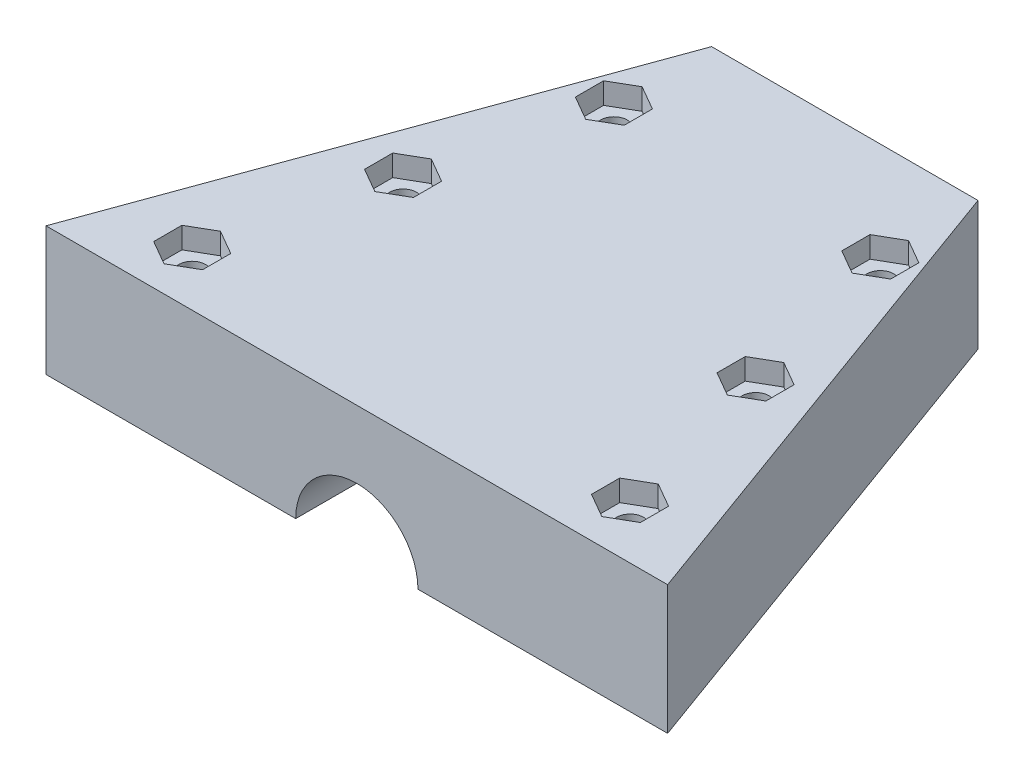
SolidWorks part; units mm, degrees
ref_plane "Front Plane" through (0, 0, 0) normal (0, 0, 1) x (1, 0, 0)
ref_plane "Top Plane" through (0, 0, 0) normal (0, 1, 0) x (1, 0, 0)
ref_plane "Right Plane" through (0, 0, 0) normal (1, 0, 0) x (0, 0, -1)
sketch "Sketch6" plane through (0, 0, 0) normal (0, 1, 0) x (1, 0, 0)
  line L0 (-16.8369, 5.7834) -> (13.1631, 5.7834)
  line L1 (13.1631, 5.7834) -> (33.1631, -49.1662)
  line L2 (33.1631, -49.1662) -> (-36.8369, -49.1662)
  line L3 (-36.8369, -49.1662) -> (-16.8369, 5.7834)
  circle A0 centre (13.1631, -5.2166) radius 1.78
  circle A1 centre (-16.8369, -5.2166) radius 1.78
  circle A2 centre (-26.4869, -43.0491) radius 1.78
  circle A3 centre (22.8131, -43.0491) radius 1.78
  dimension "D1" = 3.56
  dimension "D3" = 3.56
  dimension "D4" = 3.56
  dimension "D5" = 3.56
  dimension "D2" = 70
  dimension "D6" = 30
  dimension "D7" = 11
  dimension "D8" = 11
  dimension "D9" = 49.3
  dimension "D10" = 10.35
  dimension "D11" = 10.35
  dimension "D12" = 30
extrude "Boss-Extrude3" add sketch "Sketch6" along normal blind 14.5 contours L3 L0 L1 L2
sketch "Sketch8" plane through (0, 0, 49.1662) normal (0, 0, 1) x (1, 0, 0)
  line L0 (33.1631, 0) -> (-36.8369, 0) construction
  circle A0 centre (-1.8369, 0) radius 6.8846
extrude "Cut-Extrude3" cut sketch "Sketch8" against normal blind 88
sketch "Sketch9" plane through (0, 14.5, 0) normal (0, 1, 0) x (1, 0, 0)
  line L1 (-21.6619, -27.3083) -> (-18.9119, -25.7206)
  line L2 (-18.9119, -25.7206) -> (-18.9119, -22.5452)
  line L3 (-18.9119, -22.5452) -> (-21.6619, -20.9574)
  line L4 (-21.6619, -20.9574) -> (-24.4119, -22.5452)
  line L5 (-24.4119, -22.5452) -> (-24.4119, -25.7206)
  line L6 (-24.4119, -25.7206) -> (-21.6619, -27.3083)
  line L7 (-26.4869, -46.2245) -> (-23.7369, -44.6368)
  line L8 (-23.7369, -44.6368) -> (-23.7369, -41.4614)
  line L9 (-23.7369, -41.4614) -> (-26.4869, -39.8737)
  line L10 (-26.4869, -39.8737) -> (-29.2369, -41.4614)
  line L11 (-29.2369, -41.4614) -> (-29.2369, -44.6368)
  line L12 (-29.2369, -44.6368) -> (-26.4869, -46.2245)
  line L13 (22.8131, -46.2245) -> (25.5631, -44.6368)
  line L14 (25.5631, -44.6368) -> (25.5631, -41.4614)
  line L15 (25.5631, -41.4614) -> (22.8131, -39.8737)
  line L16 (22.8131, -39.8737) -> (20.0631, -41.4614)
  line L17 (20.0631, -41.4614) -> (20.0631, -44.6368)
  line L18 (20.0631, -44.6368) -> (22.8131, -46.2245)
  line L19 (18.0315, -27.3083) -> (20.7815, -25.7206)
  line L20 (20.7815, -25.7206) -> (20.7815, -22.5452)
  line L21 (20.7815, -22.5452) -> (18.0315, -20.9574)
  line L22 (18.0315, -20.9574) -> (15.2815, -22.5452)
  line L23 (15.2815, -22.5452) -> (15.2815, -25.7206)
  line L24 (15.2815, -25.7206) -> (18.0315, -27.3083)
  line L25 (-16.8369, -8.3921) -> (-14.0869, -6.8044)
  line L26 (-14.0869, -6.8044) -> (-14.0869, -3.6289)
  line L27 (-14.0869, -3.6289) -> (-16.8369, -2.0412)
  line L28 (-16.8369, -2.0412) -> (-19.5869, -3.6289)
  line L29 (-19.5869, -3.6289) -> (-19.5869, -6.8044)
  line L30 (-19.5869, -6.8044) -> (-16.8369, -8.3921)
  line L31 (13.1631, -8.3921) -> (15.9131, -6.8044)
  line L32 (15.9131, -6.8044) -> (15.9131, -3.6289)
  line L33 (15.9131, -3.6289) -> (13.1631, -2.0412)
  line L34 (13.1631, -2.0412) -> (10.4131, -3.6289)
  line L35 (10.4131, -3.6289) -> (10.4131, -6.8044)
  line L36 (10.4131, -6.8044) -> (13.1631, -8.3921)
  circle A0 centre (-21.6619, -24.1329) radius 2.75 construction
  circle A1 centre (-26.4869, -43.0491) radius 2.75 construction
  circle A2 centre (22.8131, -43.0491) radius 2.75 construction
  circle A3 centre (18.0315, -24.1329) radius 2.75 construction
  circle A4 centre (-16.8369, -5.2166) radius 2.75 construction
  circle A5 centre (13.1631, -5.2166) radius 2.75 construction
  point P0 (-16.8369, -5.2166)
  point P1 (13.1631, -5.2166)
  point P3 (22.8131, -43.0491)
  point P5 (-26.4869, -43.0491)
  point P7 (18.0315, -24.1329)
  point P9 (-21.6619, -24.1329)
  dimension "D1" = 5.5
  dimension "D2" = 5.5
  dimension "D3" = 5.5
  dimension "D4" = 5.5
  dimension "D5" = 5.5
  dimension "D6" = 5.5
extrude "Cut-Extrude4" cut sketch "Sketch9" against normal blind 2.4
sketch "Sketch10" plane through (0, 0, 0) normal (0, -1, 0) x (1, 0, 0)
  line L1 (-26.4869, 39.8737) -> (-23.7369, 41.4614)
  line L2 (-23.7369, 41.4614) -> (-23.7369, 44.6368)
  line L3 (-23.7369, 44.6368) -> (-26.4869, 46.2245)
  line L4 (-26.4869, 46.2245) -> (-29.2369, 44.6368)
  line L5 (-29.2369, 44.6368) -> (-29.2369, 41.4614)
  line L6 (-29.2369, 41.4614) -> (-26.4869, 39.8737)
  line L7 (-21.6619, 20.9574) -> (-18.9119, 22.5452)
  line L8 (-18.9119, 22.5452) -> (-18.9119, 25.7206)
  line L9 (-18.9119, 25.7206) -> (-21.6619, 27.3083)
  line L10 (-21.6619, 27.3083) -> (-24.4119, 25.7206)
  line L11 (-24.4119, 25.7206) -> (-24.4119, 22.5452)
  line L12 (-24.4119, 22.5452) -> (-21.6619, 20.9574)
  line L13 (18.0315, 20.9574) -> (20.7815, 22.5452)
  line L14 (20.7815, 22.5452) -> (20.7815, 25.7206)
  line L15 (20.7815, 25.7206) -> (18.0315, 27.3083)
  line L16 (18.0315, 27.3083) -> (15.2815, 25.7206)
  line L17 (15.2815, 25.7206) -> (15.2815, 22.5452)
  line L18 (15.2815, 22.5452) -> (18.0315, 20.9574)
  line L19 (22.8131, 39.8737) -> (25.5631, 41.4614)
  line L20 (25.5631, 41.4614) -> (25.5631, 44.6368)
  line L21 (25.5631, 44.6368) -> (22.8131, 46.2245)
  line L22 (22.8131, 46.2245) -> (20.0631, 44.6368)
  line L23 (20.0631, 44.6368) -> (20.0631, 41.4614)
  line L24 (20.0631, 41.4614) -> (22.8131, 39.8737)
  line L25 (-16.8369, 2.0412) -> (-14.0869, 3.6289)
  line L26 (-14.0869, 3.6289) -> (-14.0869, 6.8044)
  line L27 (-14.0869, 6.8044) -> (-16.8369, 8.3921)
  line L28 (-16.8369, 8.3921) -> (-19.5869, 6.8044)
  line L29 (-19.5869, 6.8044) -> (-19.5869, 3.6289)
  line L30 (-19.5869, 3.6289) -> (-16.8369, 2.0412)
  line L31 (13.1631, 2.0412) -> (15.9131, 3.6289)
  line L32 (15.9131, 3.6289) -> (15.9131, 6.8044)
  line L33 (15.9131, 6.8044) -> (13.1631, 8.3921)
  line L34 (13.1631, 8.3921) -> (10.4131, 6.8044)
  line L35 (10.4131, 6.8044) -> (10.4131, 3.6289)
  line L36 (10.4131, 3.6289) -> (13.1631, 2.0412)
  circle A0 centre (-26.4869, 43.0491) radius 2.75 construction
  circle A1 centre (-21.6619, 24.1329) radius 2.75 construction
  circle A2 centre (18.0315, 24.1329) radius 2.75 construction
  circle A3 centre (22.8131, 43.0491) radius 2.75 construction
  circle A4 centre (-16.8369, 5.2166) radius 2.75 construction
  circle A5 centre (13.1631, 5.2166) radius 2.75 construction
  dimension "D1" = 5.5
  dimension "D2" = 5.5
  dimension "D3" = 5.5
  dimension "D4" = 5.5
extrude "Cut-Extrude5" cut sketch "Sketch10" against normal blind 2.4
hole_wizard "#39 (0.11811024) Diameter Hole1" positions "3DSketch1" profile "Sketch13" hole size "#39" standard "ANSI Inch" end condition through all
sketch3d "3DSketch1"
  point P0 (-16.8369, 14.5, 5.2166)
  point P3 (13.1631, 14.5, 5.2166)
  point P6 (18.0315, 14.5, 24.1329)
  point P9 (-21.6619, 14.5, 24.1329)
  point P12 (-26.4869, 14.5, 43.0491)
  point P15 (22.8131, 14.5, 43.0491)
sketch "Sketch13" plane through (-16.8369, 14.5, 5.2166) normal (1, 0, 0) x (0, 0, 1)
  line L0 (0, 0) -> (0, 14.5)
  line L1 (0, 14.5) -> (1.5, 14.5)
  line L2 (1.5, 14.5) -> (1.5, 0)
  line L5 (1.5, 0) -> (0, 0)
  line L11 (0, -6.35) -> (0, 107.95) construction
  dimension "Thru Hole Dia." = 3
  dimension "Thru Hole Depth" = 14.5
